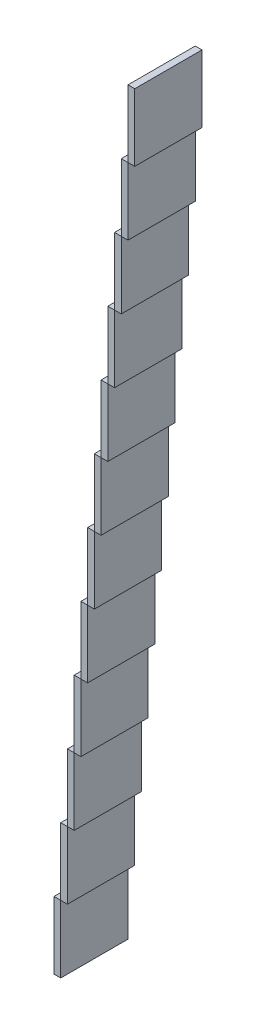
SolidWorks part; units mm, degrees
ref_plane "Front Plane" through (0, 0, 0) normal (0, 0, 1) x (1, 0, 0)
ref_plane "Top Plane" through (0, 0, 0) normal (0, 1, 0) x (1, 0, 0)
ref_plane "Right Plane" through (0, 0, 0) normal (1, 0, 0) x (0, 0, -1)
sketch "Sketch2" plane through (0, 0, 0) normal (0, 0, 1) x (1, 0, 0)
  line L0 (4.7639, 10.4456) -> (5.7639, 10.4456)
  line L1 (4.7639, 0.4456) -> (5.7639, 0.4456)
  line L2 (4.7639, 0.4456) -> (4.7639, 10.4456)
  line L48 (5.7639, 10.4456) -> (6.7639, 10.4456)
  line L50 (5.7639, 0.4456) -> (5.7639, 10.4456)
  line L53 (5.7639, 10.4456) -> (5.7639, 20.4456)
  line L54 (5.7639, 20.4456) -> (6.7639, 20.4456)
  line L55 (6.7639, 10.4456) -> (6.7639, 20.4456)
  line L59 (6.7639, 20.4456) -> (6.7639, 30.4456)
  line L104 (6.7639, 20.4456) -> (7.7639, 20.4456)
  line L106 (6.7639, 30.4456) -> (7.7639, 30.4456)
  line L107 (7.7639, 20.4456) -> (7.7639, 30.4456)
  line L111 (7.7639, 30.4456) -> (7.7639, 40.4456)
  line L156 (7.7639, 30.4456) -> (8.7639, 30.4456)
  line L158 (7.7639, 40.4456) -> (8.7639, 40.4456)
  line L159 (8.7639, 30.4456) -> (8.7639, 40.4456)
  line L208 (8.7639, 40.4456) -> (9.7639, 40.4456)
  line L209 (8.7639, 40.4456) -> (8.7639, 50.4456)
  line L210 (8.7639, 50.4456) -> (9.7639, 50.4456)
  line L215 (9.7639, 50.4456) -> (9.7639, 60.4456)
  line L257 (9.7639, 40.4456) -> (9.7639, 50.4456)
  line L260 (9.7639, 50.4456) -> (10.7639, 50.4456)
  line L262 (9.7639, 60.4456) -> (10.7639, 60.4456)
  line L263 (10.7639, 50.4456) -> (10.7639, 60.4456)
  line L267 (10.7639, 60.4456) -> (10.7639, 70.4456)
  line L312 (10.7639, 60.4456) -> (11.7639, 60.4456)
  line L314 (10.7639, 70.4456) -> (11.7639, 70.4456)
  line L315 (11.7639, 60.4456) -> (11.7639, 70.4456)
  line L319 (11.7639, 70.4456) -> (11.7639, 80.4456)
  line L364 (11.7639, 70.4456) -> (12.7639, 70.4456)
  line L366 (11.7639, 80.4456) -> (12.7639, 80.4456)
  line L367 (12.7639, 70.4456) -> (12.7639, 80.4456)
  line L371 (12.7639, 80.4456) -> (12.7639, 90.4456)
  line L416 (12.7639, 80.4456) -> (13.7639, 80.4456)
  line L418 (12.7639, 90.4456) -> (13.7639, 90.4456)
  line L419 (13.7639, 80.4456) -> (13.7639, 90.4456)
  line L423 (13.7639, 90.4456) -> (13.7639, 100.4456)
  line L468 (13.7639, 90.4456) -> (14.7639, 90.4456)
  line L471 (14.7639, 90.4456) -> (14.7639, 100.4456)
  line L472 (13.7639, 100.4456) -> (14.7639, 100.4456)
  line L475 (14.7639, 100.4456) -> (14.7639, 110.4456)
  line L520 (14.7639, 100.4456) -> (15.7639, 100.4456)
  line L522 (14.7639, 110.4456) -> (15.7639, 110.4456)
  line L523 (15.7639, 100.4456) -> (15.7639, 110.4456)
  line L527 (15.7639, 110.4456) -> (15.7639, 120.4456)
  line L572 (15.7639, 110.4456) -> (16.7639, 110.4456)
  line L574 (15.7639, 120.4456) -> (16.7639, 120.4456)
  line L575 (16.7639, 110.4456) -> (16.7639, 120.4456)
  line L576 (5.7639, 0.4456) -> (6.7639, 0.4456)
  line L577 (6.7639, 0.4456) -> (6.7639, 10.4456)
  line L578 (6.7639, 0.4456) -> (6.7639, 10.4456)
  line L579 (7.7639, 0.4456) -> (7.7639, 10.4456)
  line L580 (7.7639, 0.4456) -> (7.7639, 10.4456)
  line L581 (8.7639, 0.4456) -> (8.7639, 10.4456)
  line L582 (8.7639, 0.4456) -> (8.7639, 10.4456)
  line L583 (9.7639, 0.4456) -> (9.7639, 10.4456)
  line L584 (9.7639, 0.4456) -> (9.7639, 10.4456)
  line L585 (10.7639, 0.4456) -> (10.7639, 10.4456)
  line L586 (10.7639, 0.4456) -> (10.7639, 10.4456)
  line L587 (11.7639, 0.4456) -> (11.7639, 10.4456)
  line L588 (11.7639, 0.4456) -> (11.7639, 10.4456)
  line L589 (12.7639, 0.4456) -> (12.7639, 10.4456)
  line L590 (12.7639, 0.4456) -> (12.7639, 10.4456)
  line L591 (13.7639, 0.4456) -> (13.7639, 10.4456)
  line L592 (13.7639, 0.4456) -> (13.7639, 10.4456)
  line L593 (14.7639, 0.4456) -> (14.7639, 10.4456)
  line L594 (14.7639, 0.4456) -> (14.7639, 10.4456)
  line L595 (15.7639, 0.4456) -> (15.7639, 10.4456)
  line L596 (15.7639, 0.4456) -> (15.7639, 10.4456)
  line L597 (16.7639, 0.4456) -> (16.7639, 10.4456)
  line L598 (14.7639, 0.4456) -> (15.7639, 0.4456)
  line L599 (7.7639, 0.4456) -> (8.7639, 0.4456)
  line L600 (8.7639, 0.4456) -> (9.7639, 0.4456)
  line L601 (6.7639, 0.4456) -> (7.7639, 0.4456)
  line L602 (9.7639, 0.4456) -> (10.7639, 0.4456)
  line L603 (10.7639, 0.4456) -> (11.7639, 0.4456)
  line L604 (11.7639, 0.4456) -> (12.7639, 0.4456)
  line L605 (12.7639, 0.4456) -> (13.7639, 0.4456)
  line L606 (13.7639, 0.4456) -> (14.7639, 0.4456)
  line L607 (4.7639, 10.4456) -> (4.7639, 20.4456)
  line L608 (4.7639, 20.4456) -> (5.7639, 20.4456)
  line L609 (4.7639, 20.4456) -> (5.7639, 20.4456)
  line L610 (5.7639, 20.4456) -> (5.7639, 30.4456)
  line L612 (4.7639, 20.4456) -> (4.7639, 30.4456)
  line L613 (6.7639, 10.4456) -> (7.7639, 10.4456)
  line L614 (6.7639, 10.4456) -> (7.7639, 10.4456)
  line L615 (7.7639, 10.4456) -> (7.7639, 20.4456)
  line L616 (8.7639, 10.4456) -> (8.7639, 20.4456)
  line L617 (9.7639, 10.4456) -> (9.7639, 20.4456)
  line L618 (10.7639, 10.4456) -> (10.7639, 20.4456)
  line L619 (11.7639, 10.4456) -> (11.7639, 20.4456)
  line L620 (12.7639, 10.4456) -> (12.7639, 20.4456)
  line L621 (13.7639, 10.4456) -> (13.7639, 20.4456)
  line L622 (14.7639, 10.4456) -> (14.7639, 20.4456)
  line L623 (15.7639, 10.4456) -> (15.7639, 20.4456)
  line L624 (16.7639, 10.4456) -> (16.7639, 20.4456)
  line L625 (15.7639, 10.4456) -> (16.7639, 10.4456)
  line L626 (15.7639, 10.4456) -> (16.7639, 10.4456)
  line L627 (14.7639, 10.4456) -> (15.7639, 10.4456)
  line L628 (14.7639, 10.4456) -> (15.7639, 10.4456)
  line L629 (13.7639, 10.4456) -> (14.7639, 10.4456)
  line L630 (13.7639, 10.4456) -> (14.7639, 10.4456)
  line L631 (10.7639, 10.4456) -> (11.7639, 10.4456)
  line L632 (10.7639, 10.4456) -> (11.7639, 10.4456)
  line L633 (9.7639, 10.4456) -> (10.7639, 10.4456)
  line L634 (9.7639, 10.4456) -> (10.7639, 10.4456)
  line L635 (8.7639, 10.4456) -> (9.7639, 10.4456)
  line L636 (8.7639, 10.4456) -> (9.7639, 10.4456)
  line L637 (7.7639, 10.4456) -> (8.7639, 10.4456)
  line L638 (7.7639, 10.4456) -> (8.7639, 10.4456)
  line L639 (11.7639, 10.4456) -> (12.7639, 10.4456)
  line L640 (11.7639, 10.4456) -> (12.7639, 10.4456)
  line L641 (12.7639, 10.4456) -> (13.7639, 10.4456)
  line L642 (12.7639, 10.4456) -> (13.7639, 10.4456)
  line L674 (5.7639, 30.4456) -> (5.7639, 40.4456)
  line L678 (4.7639, 30.4456) -> (5.7639, 30.4456)
  line L679 (4.7639, 30.4456) -> (5.7639, 30.4456)
  line L680 (4.7639, 30.4456) -> (4.7639, 40.4456)
  line L687 (5.7639, 40.4456) -> (5.7639, 50.4456)
  line L689 (4.7639, 40.4456) -> (4.7639, 50.4456)
  line L692 (4.7639, 40.4456) -> (5.7639, 40.4456)
  line L693 (4.7639, 40.4456) -> (5.7639, 40.4456)
  line L700 (5.7639, 50.4456) -> (5.7639, 60.4456)
  line L702 (4.7639, 50.4456) -> (4.7639, 60.4456)
  line L703 (4.7639, 50.4456) -> (5.7639, 50.4456)
  line L704 (4.7639, 50.4456) -> (5.7639, 50.4456)
  line L717 (5.7639, 60.4456) -> (5.7639, 70.4456)
  line L719 (4.7639, 60.4456) -> (4.7639, 70.4456)
  line L724 (4.7639, 60.4456) -> (5.7639, 60.4456)
  line L725 (4.7639, 60.4456) -> (5.7639, 60.4456)
  line L782 (5.7639, 70.4456) -> (5.7639, 80.4456)
  line L784 (4.7639, 70.4456) -> (4.7639, 80.4456)
  line L785 (4.7639, 80.4456) -> (5.7639, 80.4456)
  line L786 (4.7639, 80.4456) -> (5.7639, 80.4456)
  line L787 (5.7639, 80.4456) -> (5.7639, 90.4456)
  line L793 (4.7639, 80.4456) -> (4.7639, 90.4456)
  line L794 (4.7639, 70.4456) -> (5.7639, 70.4456)
  line L795 (4.7639, 70.4456) -> (5.7639, 70.4456)
  line L832 (4.7639, 120.4456) -> (5.7639, 120.4456)
  line L833 (4.7639, 110.4456) -> (4.7639, 120.4456)
  line L834 (5.7639, 110.4456) -> (5.7639, 120.4456)
  line L856 (5.7639, 100.4456) -> (5.7639, 110.4456)
  line L858 (4.7639, 110.4456) -> (5.7639, 110.4456)
  line L859 (4.7639, 110.4456) -> (5.7639, 110.4456)
  line L861 (4.7639, 100.4456) -> (4.7639, 110.4456)
  line L879 (5.7639, 90.4456) -> (5.7639, 100.4456)
  line L881 (4.7639, 100.4456) -> (5.7639, 100.4456)
  line L882 (4.7639, 100.4456) -> (5.7639, 100.4456)
  line L898 (4.7639, 90.4456) -> (5.7639, 90.4456)
  line L899 (4.7639, 90.4456) -> (5.7639, 90.4456)
  line L900 (4.7639, 90.4456) -> (4.7639, 100.4456)
  line L901 (15.7639, 0.4456) -> (16.7639, 0.4456)
  dimension "D3" = 12
  dimension "D4" = 12
extrude "Boss-Extrude1" add sketch "Sketch2" along normal blind 10
